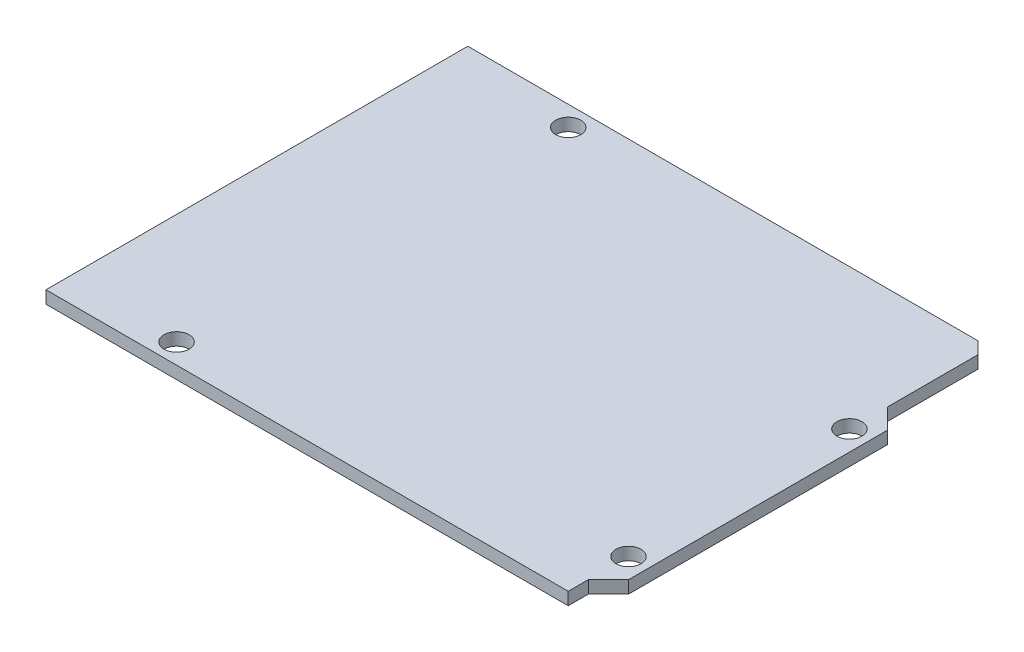
SolidWorks part; units mm, degrees
material "FR-4 Fiberglass"
ref_plane "Front Plane" through (0, 0, 0) normal (0, 0, 1) x (1, 0, 0)
ref_plane "Top Plane" through (0, 0, 0) normal (0, 1, 0) x (1, 0, 0)
ref_plane "Right Plane" through (0, 0, 0) normal (1, 0, 0) x (0, 0, -1)
sketch "Sketch1" plane through (0, 0, 0) normal (0, 1, 0) x (1, 0, 0)
  line L0 (0, 0) -> (0, 53.34)
  line L1 (0, 53.34) -> (64.516, 53.34)
  line L2 (64.516, 53.34) -> (66.04, 51.816)
  line L3 (66.04, 51.816) -> (66.04, 40.386)
  line L4 (66.04, 40.386) -> (68.58, 37.846)
  line L5 (68.58, 37.846) -> (68.58, 5.08)
  line L6 (68.58, 5.08) -> (66.04, 2.54)
  line L7 (66.04, 0) -> (0, 0)
  line L8 (66.04, 2.54) -> (66.04, 0)
  dimension "D1" = 53.34
  dimension "D2" = 64.516
  dimension "D3" = 66.04
  dimension "D4" = 66.04
  dimension "D5" = 68.58
  dimension "D6" = 51.816
  dimension "D7" = 40.386
  dimension "D8" = 37.846
  dimension "D9" = 5.08
extrude "Boss-Extrude1" add sketch "Sketch1" along normal blind 1.5875
hole_wizard "1/8 (0.125) Diameter Hole1" positions "Sketch3" profile "Sketch2" hole size "1/8" standard "ANSI Inch" end condition through all
sketch "Sketch3" plane through (0, 1.5875, 0) normal (0, 1, 0) x (1, 0, 0)
  line L0 (0, 0) -> (66.04, 0) construction
  line L1 (0, 53.34) -> (0, 0) construction
  line L2 (66.04, 35.56) -> (66.04, 7.62) construction
  point P0 (13.97, 2.54)
  point P2 (15.24, 50.8)
  point P4 (66.04, 35.56)
  point P6 (66.04, 7.62)
  dimension "D1" = 2.54
  dimension "D2" = 13.97
  dimension "D3" = 50.8
  dimension "D4" = 15.24
  dimension "D5" = 66.04
  dimension "D6" = 35.56
  dimension "D7" = 7.62
sketch "Sketch2" plane through (13.97, 1.5875, -2.54) normal (1, 0, 0) x (0, 0, 1)
  line L0 (0, 0) -> (0, 1.5875)
  line L1 (0, 1.5875) -> (1.5875, 1.5875)
  line L2 (1.5875, 1.5875) -> (1.5875, 0)
  line L5 (1.5875, 0) -> (0, 0)
  line L11 (0, -6.35) -> (0, 107.95) construction
  dimension "Thru Hole Dia." = 3.175
  dimension "Thru Hole Depth" = 1.5875
